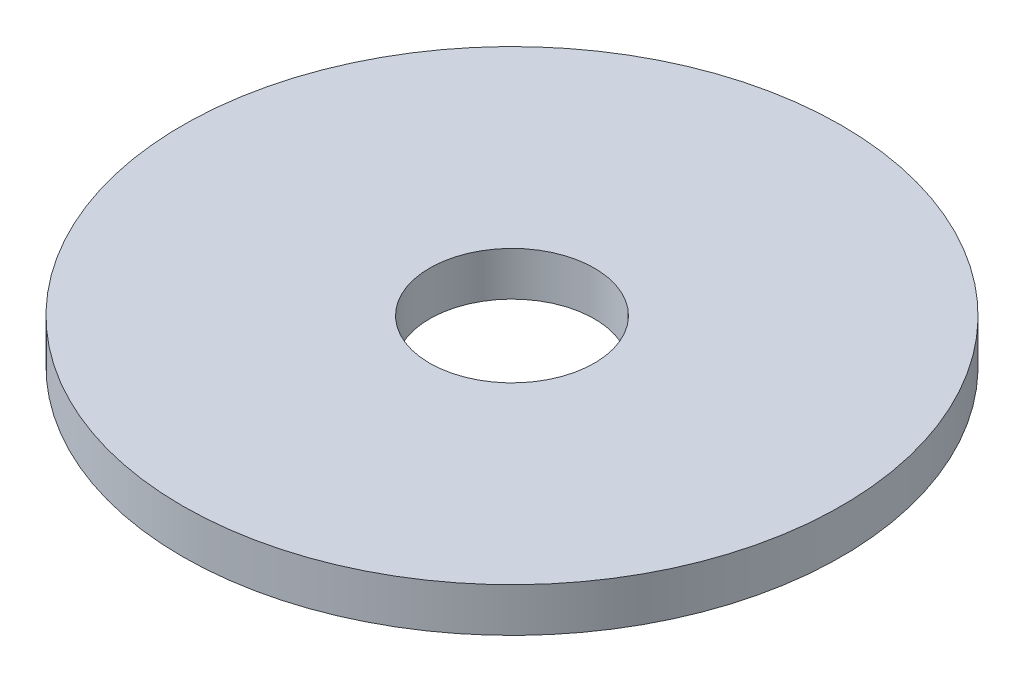
SolidWorks part; units mm, degrees
ref_plane "Front Plane" through (0, 0, 0) normal (0, 0, 1) x (1, 0, 0)
ref_plane "Top Plane" through (0, 0, 0) normal (0, 1, 0) x (1, 0, 0)
ref_plane "Right Plane" through (0, 0, 0) normal (1, 0, 0) x (0, 0, -1)
sketch "Sketch1" plane through (0, 0, 0) normal (0, 1, 0) x (1, 0, 0)
  circle A0 centre (0, 0) radius 1.875
  circle A1 centre (0, 0) radius 7.5
extrude "Boss-Extrude1" add sketch "Sketch1" along normal mid plane 1
